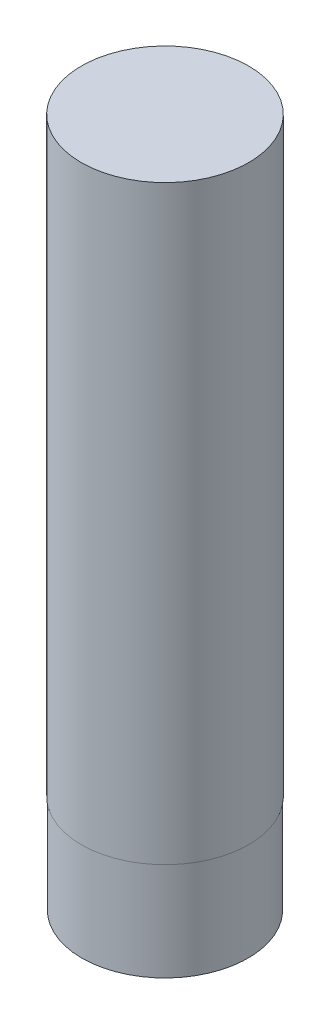
SolidWorks part; units mm, degrees
ref_plane "Front Plane" through (0, 0, 0) normal (0, 0, 1) x (1, 0, 0)
ref_plane "Top Plane" through (0, 0, 0) normal (0, 1, 0) x (1, 0, 0)
ref_plane "Right Plane" through (0, 0, 0) normal (1, 0, 0) x (0, 0, -1)
sketch "Sketch1" plane through (0, 0, 0) normal (0, 1, 0) x (1, 0, 0)
  circle A0 centre (0, 0) radius 8.5
  dimension "D1" = 17
extrude "Boss-Extrude1" add sketch "Sketch1" along normal blind 60
sketch "Sketch2" plane through (0, 0, 0) normal (0, -1, 0) x (1, 0, 0)
  circle A0 centre (0, 0) radius 8.45
  dimension "D1" = 16.9
extrude "Boss-Extrude2" add sketch "Sketch2" along normal blind 10
